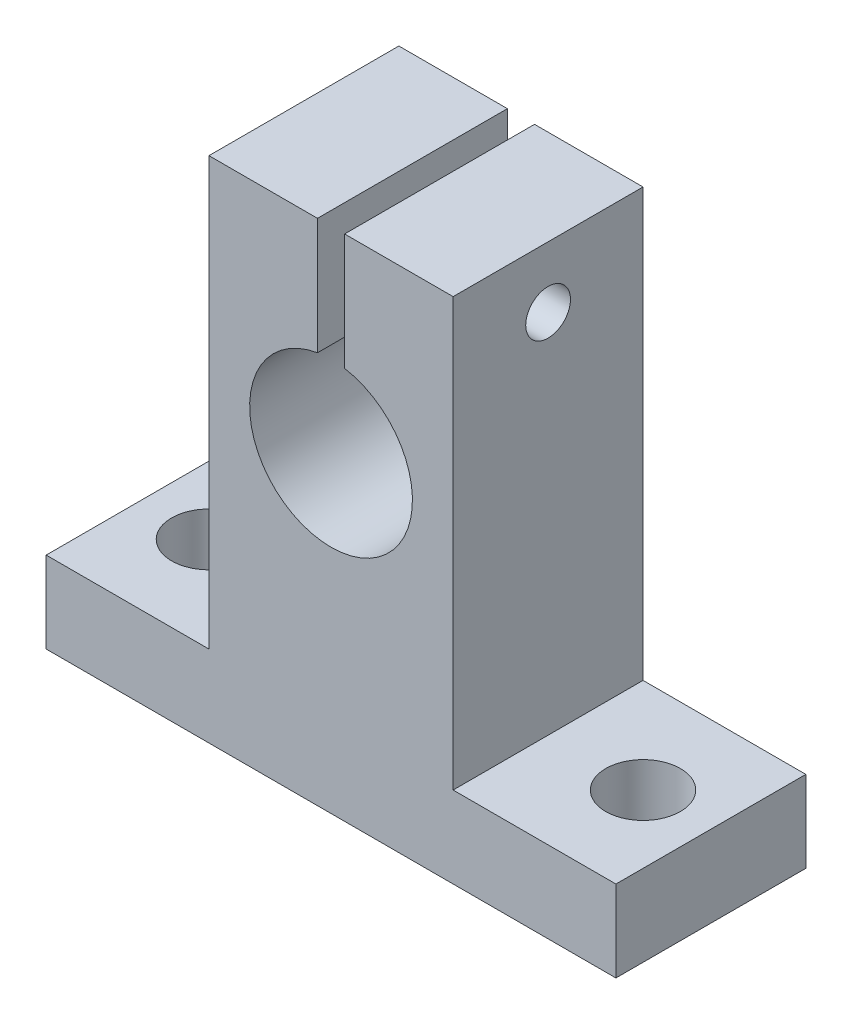
SolidWorks part; units mm, degrees
ref_plane "Płaszczyzna przednia" through (0, 0, 0) normal (0, 0, 1) x (1, 0, 0)
ref_plane "Płaszczyzna górna" through (0, 0, 0) normal (0, 1, 0) x (1, 0, 0)
ref_plane "Płaszczyzna prawa" through (0, 0, 0) normal (1, 0, 0) x (0, 0, -1)
sketch "Sketch2" plane through (0, 0, 0) normal (0, 0, 1) x (1, 0, 0)
  line L0 (-1, 0) -> (-1, 14.5)
  line L1 (-1, 14.5) -> (-9, 14.5)
  line L2 (-9, 14.5) -> (-9, -17)
  line L3 (-9, -17) -> (-21, -17)
  line L4 (-21, -17) -> (-21, -23)
  line L5 (-21, -23) -> (0, -23)
  line L6 (0, -23) -> (0, 0)
  line L7 (0, 0) -> (-1, 0)
  dimension "D1" = 9
  dimension "D2" = 1
  dimension "D3" = 23
  dimension "D4" = 37.5
  dimension "D5" = 6
  dimension "D6" = 21
extrude "Boss-Extrude1" add sketch "Sketch2" along normal blind 14 contours L6 L7 L0 L1 L2 L3 L4 L5
mirror "Mirror1" about plane through (0, -23, 14) normal (-1, 0, 0) of "Boss-Extrude1"
hole_wizard "Tap Drill for M4x0.7 Tap2" positions "Sketch5" profile "Sketch6" hole size "M4x0.7" standard "ANSI Metric" end condition through all
sketch "Sketch5" plane through (-9, 0, 0) normal (-1, 0, 0) x (0, 0, 1)
  line L0 (14, 14.5) -> (0, 14.5) construction
  point P0 (7, 10)
  point P10 (7, 14.5)
  dimension "D1" = 10
sketch "Sketch6" plane through (-9, 10, 7) normal (0, 1, 0) x (0, 0, 1)
  line L0 (0, 0) -> (0, 30)
  line L1 (0, 30) -> (1.65, 30)
  line L2 (1.65, 30) -> (1.65, 0)
  line L5 (1.65, 0) -> (0, 0)
  line L11 (0, -6.35) -> (0, 107.95) construction
  dimension "Thru Hole Dia." = 3.3
  dimension "Thru Hole Depth" = 30
hole_wizard "Ø12.0 (12) Diameter Hole1" positions "Sketch9" profile "Sketch10" hole size "Ø12.0" standard "ANSI Metric" end condition through all
sketch "Sketch9" plane through (0, 0, 0) normal (0, 0, 1) x (1, 0, 0)
  point P0 (0, 0)
sketch "Sketch10" plane through (0, 0, 0) normal (1, 0, 0) x (0, 1, 0)
  line L0 (0, 0) -> (0, 14)
  line L1 (0, 14) -> (6, 14)
  line L2 (6, 14) -> (6, 0)
  line L5 (6, 0) -> (0, 0)
  line L11 (0, -6.35) -> (0, 107.95) construction
  dimension "Thru Hole Dia." = 12
  dimension "Thru Hole Depth" = 14
hole_wizard "Tap Drill for M5x0.8 Tap1" positions "Sketch11" profile "Sketch12" hole size "M5x0.8" standard "ANSI Metric" end condition through all
sketch "Sketch11" plane through (0, -23, 0) normal (0, -1, 0) x (-1, 0, 0)
  line L0 (-16, -7) -> (16, -7) construction
  line L2 (-21, -14) -> (-21, 0) construction
  point P0 (-16, -7)
  point P2 (16, -7)
  point P10 (0, -7)
  point P14 (-21, -7)
  dimension "D1" = 32
sketch "Sketch12" plane through (16, -23, 7) normal (1, 0, 0) x (0, 0, -1)
  line L0 (0, 0) -> (0, 37.5)
  line L1 (0, 37.5) -> (2.75, 37.5)
  line L2 (2.75, 37.5) -> (2.75, 0)
  line L5 (2.75, 0) -> (0, 0)
  line L11 (0, -6.35) -> (0, 107.95) construction
  dimension "Thru Hole Dia." = 5.5
  dimension "Thru Hole Depth" = 37.5
